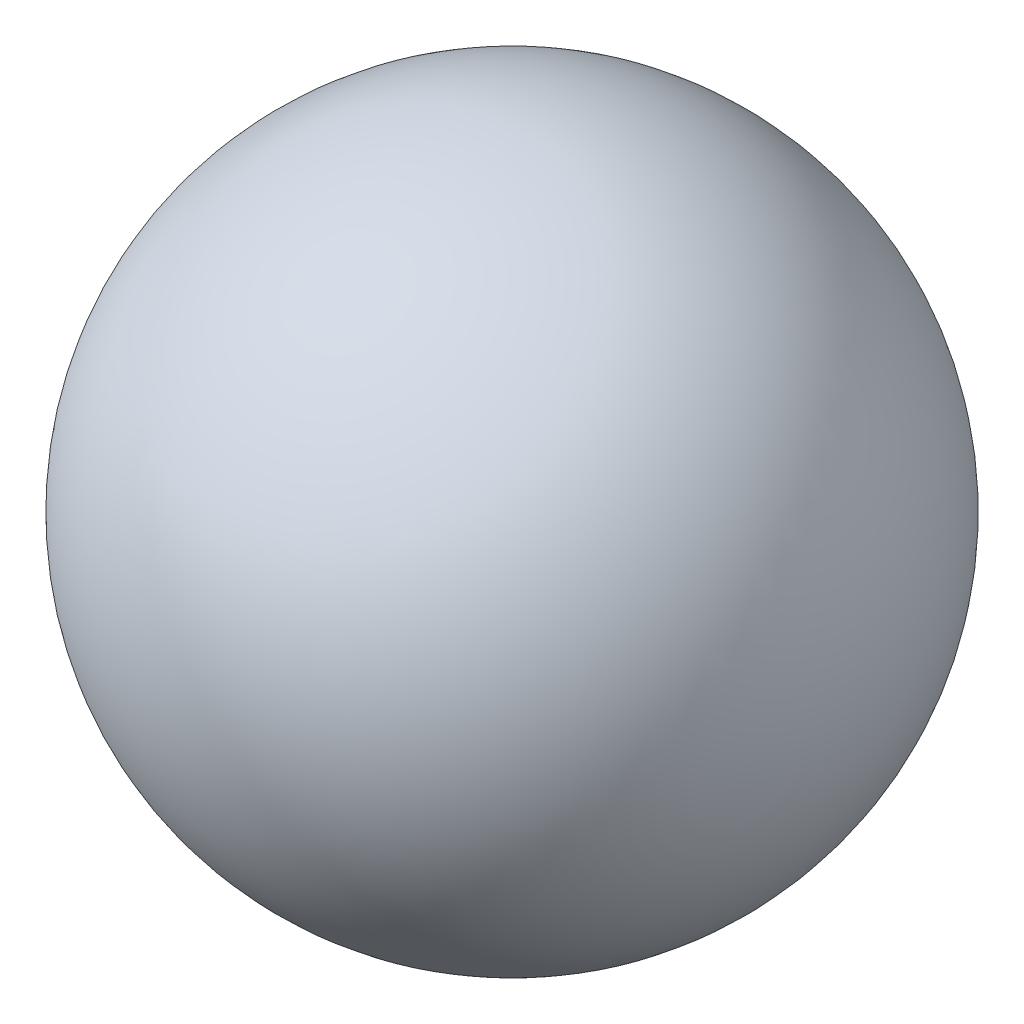
SolidWorks part; units mm, degrees
ref_plane "Front Plane" through (0, 0, 0) normal (0, 0, 1) x (1, 0, 0)
ref_plane "Top Plane" through (0, 0, 0) normal (0, 1, 0) x (1, 0, 0)
ref_plane "Right Plane" through (0, 0, 0) normal (1, 0, 0) x (0, 0, -1)
sketch "Sketch1" plane through (0, 0, 0) normal (0, 0, 1) x (1, 0, 0)
  line L0 (0, 10) -> (0, -10)
  arc A0 (0, 10) -> (0, -10) centre (0, 0) ccw
  dimension "D1" = 10
revolve "Revolve1" add sketch "Sketch1" angle 360 about L0
